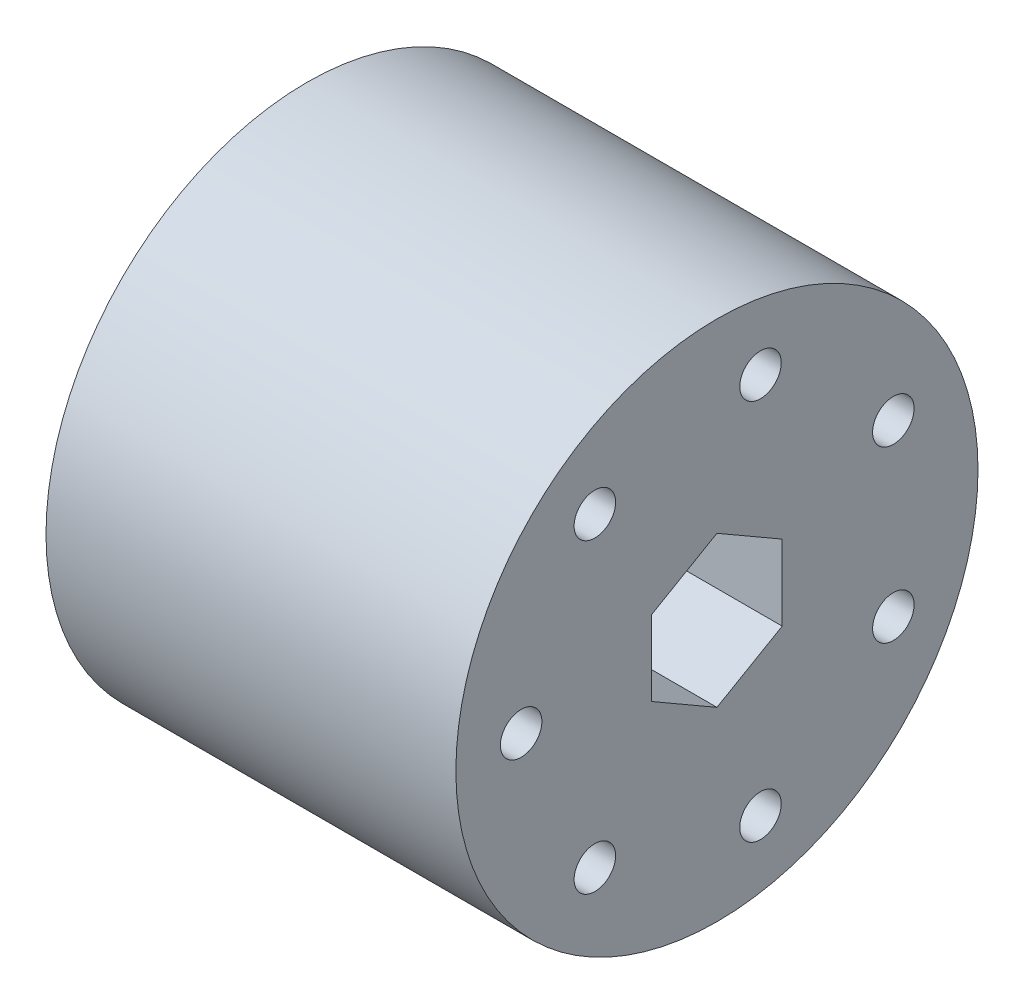
SolidWorks part; units mm, degrees
ref_plane "Front Plane" through (0, 0, 0) normal (1, 0, 0) x (0, 1, 0)
ref_plane "Top Plane" through (0, 0, 0) normal (0, 0, 1) x (0, 1, 0)
ref_plane "Right Plane" through (0, 0, 0) normal (0, 1, 0) x (-1, 0, 0)
sketch "Sketch2" plane through (0, 0, 0) normal (1, 0, 0) x (0, 1, 0)
  line L1 (3.6662, 6.35) -> (-3.6662, 6.35)
  line L2 (-3.6662, 6.35) -> (-7.3323, 0)
  line L3 (-7.3323, 0) -> (-3.6662, -6.35)
  line L4 (-3.6662, -6.35) -> (3.6662, -6.35)
  line L5 (3.6662, -6.35) -> (7.3323, 0)
  line L6 (7.3323, 0) -> (3.6662, 6.35)
  circle A0 centre (0, 0) radius 25.4
  circle A1 centre (0, 0) radius 6.35 construction
  dimension "D1" = 50.8
  dimension "D2" = 12.7
extrude "Boss-Extrude1" add sketch "Sketch2" along normal blind 39.878
sketch "Sketch5" plane through (39.878, 0, 0) normal (1, 0, 0) x (0, 1, 0)
  circle A0 centre (0, 0) radius 19.05 construction
  circle A1 centre (0, 0) radius 19.05
  circle A2 centre (0, 0) radius 19.05
  circle A3 centre (0, 0) radius 19.05
  circle A4 centre (0, 0) radius 19.05
  circle A5 centre (0, 0) radius 19.05
  circle A6 centre (0, 0) radius 19.05
  point P4 (0, 19.05)
  point P12 (14.8939, 11.8775)
  point P14 (18.5724, -4.239)
  point P16 (8.2655, -17.1635)
  point P18 (-8.2655, -17.1635)
  point P20 (-18.5724, -4.239)
  point P22 (-14.8939, 11.8775)
  dimension "D1" = 38.1
  dimension "D2" = 7
hole_wizard "Tap Drill for #10-32 Tap1" positions "Sketch5" profile "Sketch4" hole size "#10-32" standard "ANSI Inch" end condition through all
sketch "Sketch4" plane through (39.878, -14.8939, 11.8775) normal (0, 1, 0) x (0, 0, -1)
  line L0 (0, 0) -> (0, 39.878)
  line L1 (0, 39.878) -> (2.0193, 39.878)
  line L2 (2.0193, 39.878) -> (2.0193, 0)
  line L5 (2.0193, 0) -> (0, 0)
  line L11 (0, -6.35) -> (0, 107.95) construction
  dimension "Thru Hole Dia." = 4.0386
  dimension "Thru Hole Depth" = 39.878
